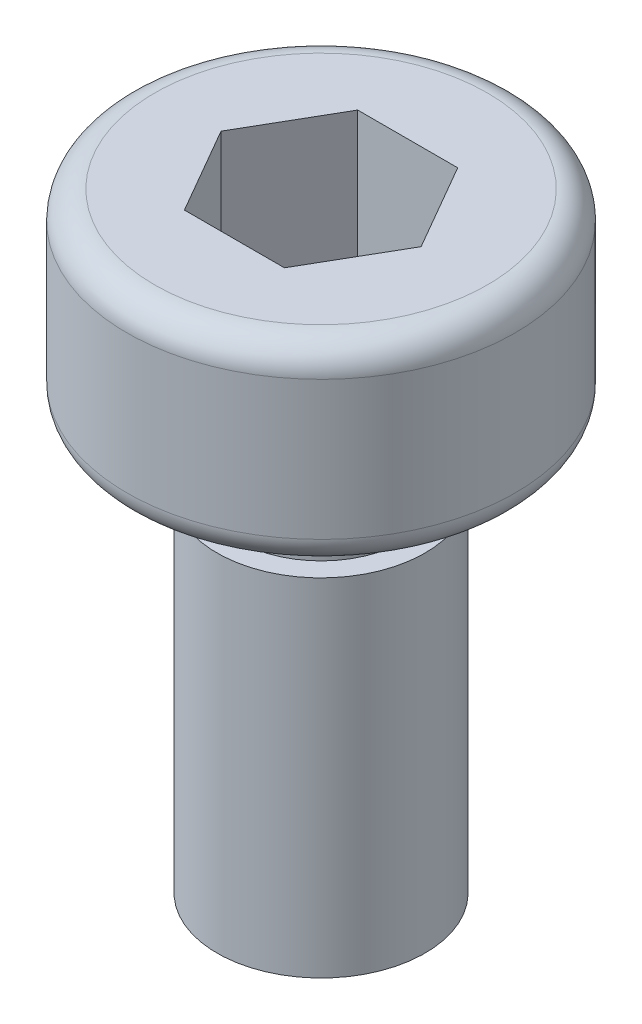
SolidWorks part; units mm, degrees
material "AISI 304"
ref_plane "前视基准面" through (0, 0, 0) normal (0, 0, 1) x (1, 0, 0)
ref_plane "上视基准面" through (0, 0, 0) normal (0, 1, 0) x (1, 0, 0)
ref_plane "右视基准面" through (0, 0, 0) normal (1, 0, 0) x (0, 0, -1)
sketch "草图1" plane through (0, 0, 0) normal (0, 0, 1) x (1, 0, 0)
  line L0 (0, 0) -> (0, 8.8) construction
  line L1 (0, 8.8) -> (-2.4, 8.8)
  line L2 (-2.8, 8.4) -> (-2.8, 6.4)
  line L3 (-2.4, 6) -> (-1.2, 6)
  line L4 (-1.2, 6) -> (-1.2, 5)
  line L5 (-1.2, 5) -> (-1.5, 5)
  line L6 (-1.5, 5) -> (-1.5, 0)
  line L7 (-1.5, 0) -> (0, 0)
  line L8 (0, 0) -> (0, 8.8)
  arc A0 (-2.8, 6.4) -> (-2.4, 6) centre (-2.4, 6.4) ccw
  arc A1 (-2.4, 8.8) -> (-2.8, 8.4) centre (-2.4, 8.4) ccw
  point P11 (-2.8, 6)
  point P14 (-2.8, 8.8)
  dimension "D7" = 0.4
  dimension "D1" = 6
  dimension "D2" = 2.8
  dimension "D3" = 5.6
  dimension "D4" = 3
  dimension "D5" = 1
  dimension "D6" = 1.2
revolve "旋转1" add sketch "草图1" angle 360 about L0
cosmetic thread "装饰螺纹线1" parameters "D2"=2.439
sketch "草图2" plane through (0, 8.8, 0) normal (0, 1, 0) x (1, 0, 0)
  line L1 (-0.7217, 1.25) -> (-1.4434, 0)
  line L2 (-1.4434, 0) -> (-0.7217, -1.25)
  line L3 (-0.7217, -1.25) -> (0.7217, -1.25)
  line L4 (0.7217, -1.25) -> (1.4434, 0)
  line L5 (1.4434, 0) -> (0.7217, 1.25)
  line L6 (0.7217, 1.25) -> (-0.7217, 1.25)
  circle A0 centre (0, 0) radius 1.25 construction
  dimension "D1" = 2.5
extrude "切除-拉伸1" cut sketch "草图2" against normal blind 2
